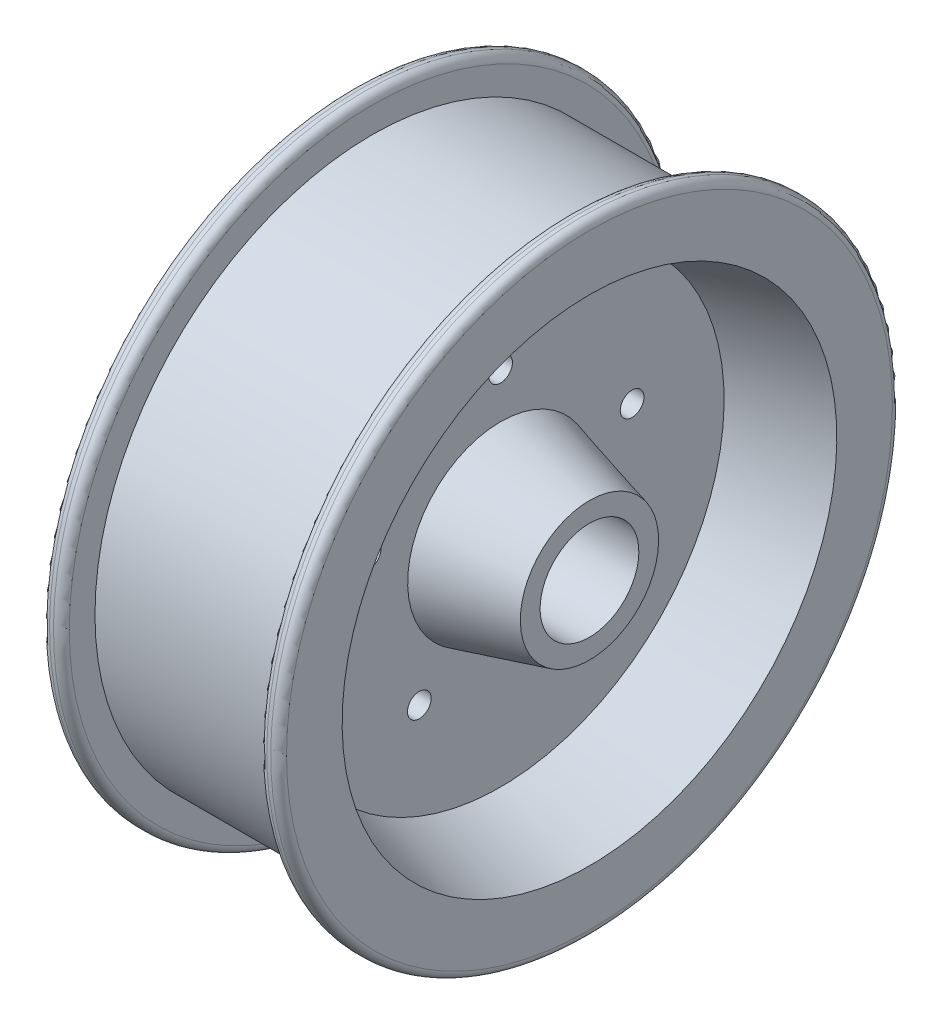
SolidWorks part; units mm, degrees
ref_plane "Front Plane" through (0, 0, 0) normal (0, 0, 1) x (1, 0, 0)
ref_plane "Top Plane" through (0, 0, 0) normal (0, 1, 0) x (1, 0, 0)
ref_plane "Right Plane" through (0, 0, 0) normal (1, 0, 0) x (0, 0, -1)
sketch "Sketch1" plane through (0, 0, 0) normal (0, 0, 1) x (1, 0, 0)
  line L0 (104.9695, 20.9836) -> (-85.3933, 20.9836) construction
  line L1 (-38.1, 36.8586) -> (38.1, 36.8586)
  line L2 (38.1, 36.8586) -> (38.1, 43.2086)
  line L3 (38.1, 43.2086) -> (9.525, 50.8653)
  line L4 (9.525, 50.8653) -> (9.525, 92.8544)
  line L5 (9.525, 92.8544) -> (38.1, 100.511)
  line L6 (38.1, 100.511) -> (38.1, 118.3886)
  line L7 (35.56, 120.9286) -> (34.29, 120.9286)
  line L8 (31.75, 118.3886) -> (31.75, 110.1336)
  line L9 (31.75, 110.1336) -> (-31.75, 110.1336)
  line L17 (0, 0) -> (0, 120.5095) construction
  line L18 (9.525, 92.8544) -> (99.5346, 92.8544) construction
  line L19 (0, 110.1336) -> (0, 36.8586)
  line L20 (-31.75, 118.3886) -> (-31.75, 110.1336)
  line L21 (-35.56, 120.9286) -> (-34.29, 120.9286)
  line L22 (-38.1, 100.511) -> (-38.1, 118.3886)
  line L23 (-9.525, 92.8544) -> (-38.1, 100.511)
  line L24 (-9.525, 50.8653) -> (-9.525, 92.8544)
  line L25 (-38.1, 43.2086) -> (-9.525, 50.8653)
  line L26 (-38.1, 36.8586) -> (-38.1, 43.2086)
  line L27 (9.525, 50.8653) -> (133.5801, 50.8653) construction
  arc A0 (34.29, 120.9286) -> (31.75, 118.3886) centre (34.29, 118.3886) ccw
  arc A1 (38.1, 118.3886) -> (35.56, 120.9286) centre (35.56, 118.3886) ccw
  arc A2 (-34.29, 120.9286) -> (-31.75, 118.3886) centre (-34.29, 118.3886) cw
  arc A3 (-38.1, 118.3886) -> (-35.56, 120.9286) centre (-35.56, 118.3886) cw
  point P3 (0, 73.4961)
  point P15 (31.75, 120.9286)
  point P18 (38.1, 120.9286)
  dimension "D10" = 2.54
  dimension "D1" = 38.1
  dimension "D2" = 38.1
  dimension "D3" = 15
  dimension "D4" = 6.35
  dimension "D5" = 57.3024
  dimension "D6" = 9.525
  dimension "D7" = 10.795
  dimension "D8" = 9.6226
  dimension "D9" = 6.35
  dimension "D11" = 15.875
  dimension "D12" = 15
revolve "Revolve2" add sketch "Sketch1" angle 360 about L0
sketch "Sketch3" plane through (9.525, 0, 0) normal (1, 0, 0) x (0, 0, -1)
  circle A2 centre (0, 65.4336) radius 3.81
  circle A5 centre (0, 20.9836) radius 15.875 construction
  dimension "D1" = 7.62
  dimension "D2" = 44.45
extrude "Cut-Extrude1" cut sketch "Sketch3" against normal up to next (19.05 mm away)
pattern_circular "CirPattern1" count 5 over 360 about axis through (0, 20.9836, 0) along (1, 0, 0) of "Cut-Extrude1"
